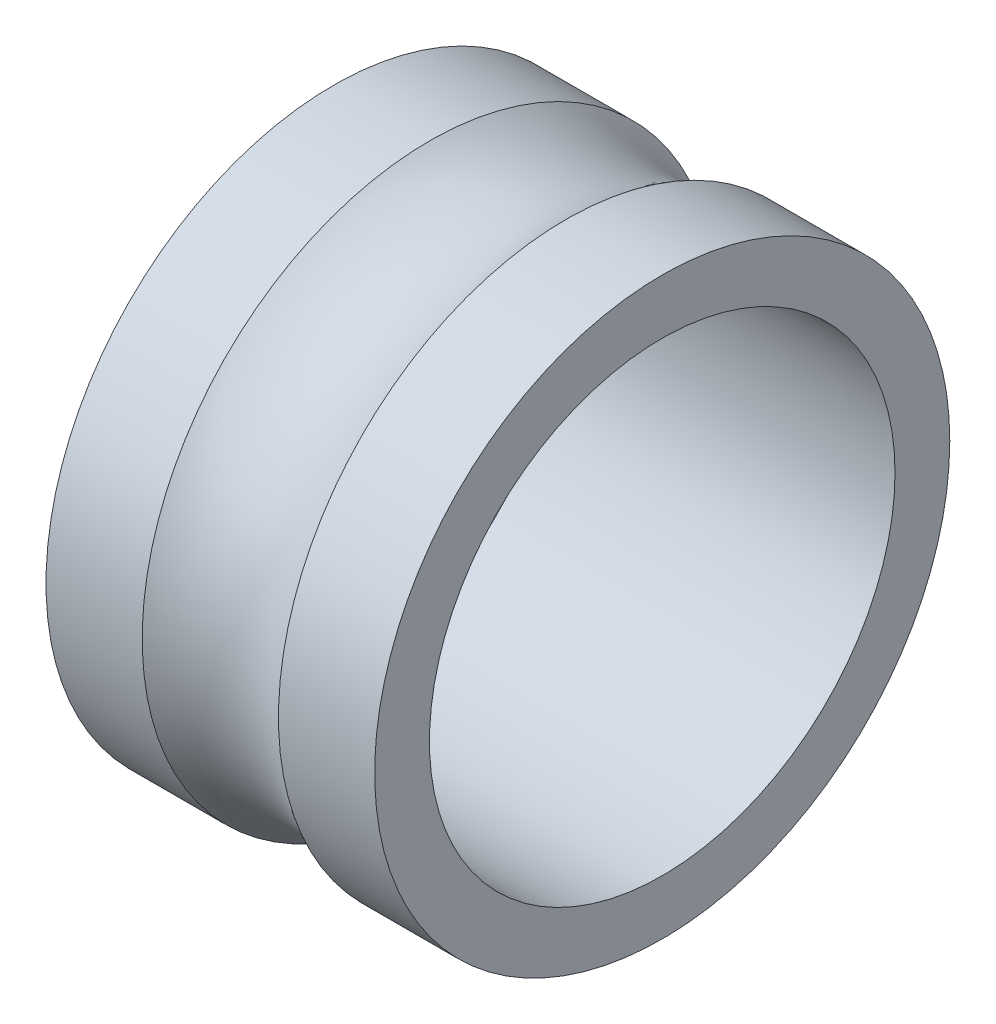
SolidWorks part; units mm, degrees
ref_plane "前视基准面" through (0, 0, 0) normal (0, 0, 1) x (1, 0, 0)
ref_plane "上视基准面" through (0, 0, 0) normal (0, 1, 0) x (1, 0, 0)
ref_plane "右视基准面" through (0, 0, 0) normal (1, 0, 0) x (0, 0, -1)
sketch "草图1" plane through (0, 0, 0) normal (0, 0, 1) x (1, 0, 0)
  line L1 (6, -5.75) -> (-6, -5.75)
  line L2 (6, -5.75) -> (6, -3.75)
  line L4 (-6, -5.75) -> (-6, -3.75)
  line L5 (0, -5.75) -> (0, -14.25) construction
  line L6 (0, -14.25) -> (-12.2343, -14.25) construction
  line L7 (6, -3.75) -> (2.4875, -3.75)
  line L10 (-2.4875, -3.75) -> (-6, -3.75)
  arc A1 (-2.4875, -3.75) -> (2.4875, -3.75) centre (0, 0) ccw
  point P0 (0, 0)
  dimension "D1" = 8.5
  dimension "D2" = 12
  dimension "D5" = 2
revolve "旋转1" add sketch "草图1" angle 360 about L6
